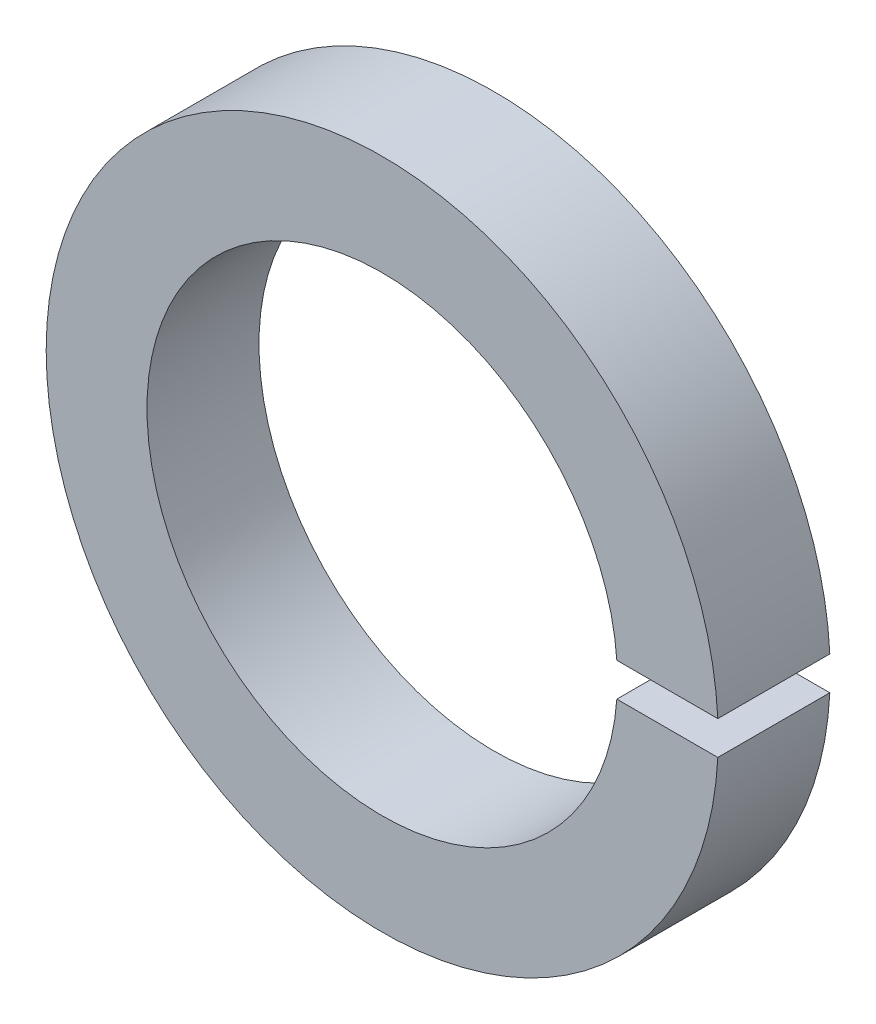
SolidWorks part; units mm, degrees
ref_plane "Front Plane" through (0, 0, 0) normal (0, 0, 1) x (1, 0, 0)
ref_plane "Top Plane" through (0, 0, 0) normal (0, 1, 0) x (1, 0, 0)
ref_plane "Right Plane" through (0, 0, 0) normal (1, 0, 0) x (0, 0, -1)
sketch "Sketch1" plane through (0, 0, 0) normal (0, 0, 1) x (1, 0, 0)
  circle A0 centre (0, 0) radius 15
  circle A1 centre (0, 0) radius 10.5
  dimension "D1" = 30
  dimension "D2" = 21
extrude "Boss-Extrude1" add sketch "Sketch1" along normal blind 5
sketch "Sketch3" plane through (0, 0, 0) normal (0, 0, -1) x (-1, 0, 0)
  line L0 (-25.8441, 0) -> (-5.2827, 0) construction
  line L1 (55, 0) -> (-55, 0) construction
  line L3 (-15.5634, 0.75) -> (-9.6952, 0.75)
  line L4 (-15.5634, 0.75) -> (-15.5634, -0.75)
  line L5 (-15.5634, -0.75) -> (-9.6952, -0.75)
  line L6 (-9.6952, 0.75) -> (-9.6952, -0.75)
  point P9 (-15.5634, 0)
  dimension "D1" = 1.5
  dimension "D2" = 5.8682
extrude "Cut-Extrude1" cut sketch "Sketch3" against normal through all
